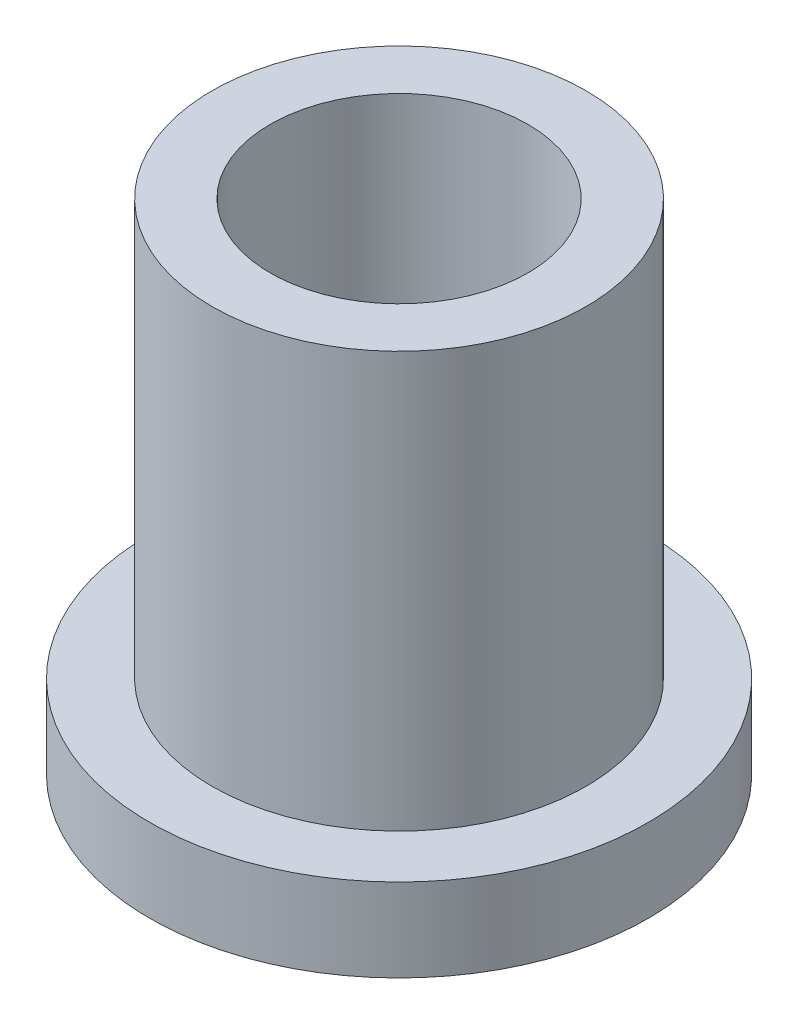
SolidWorks part; units mm, degrees
material "ПТФЭ (общий)"
ref_plane "Спереди" through (0, 0, 0) normal (0, 0, 1) x (1, 0, 0)
ref_plane "Сверху" through (0, 0, 0) normal (0, 1, 0) x (1, 0, 0)
ref_plane "Справа" through (0, 0, 0) normal (1, 0, 0) x (0, 0, -1)
sketch "Эскиз1" plane through (0, 0, 0) normal (0, 0, 1) x (1, 0, 0)
  line L0 (0, 0) -> (0, 9.9301) construction
  line L1 (1.55, 6) -> (1.55, 0)
  line L2 (1.55, 0) -> (3, 0)
  line L3 (3, 0) -> (3, 1)
  line L4 (3, 1) -> (2.25, 1)
  line L5 (2.25, 1) -> (2.25, 6)
  line L6 (2.25, 6) -> (1.55, 6)
  dimension "D1" = 3.1
  dimension "D2" = 4.5
  dimension "D3" = 6
  dimension "D4" = 1
  dimension "D5" = 6
revolve "Повернуть1" add sketch "Эскиз1" angle 360 about L0
